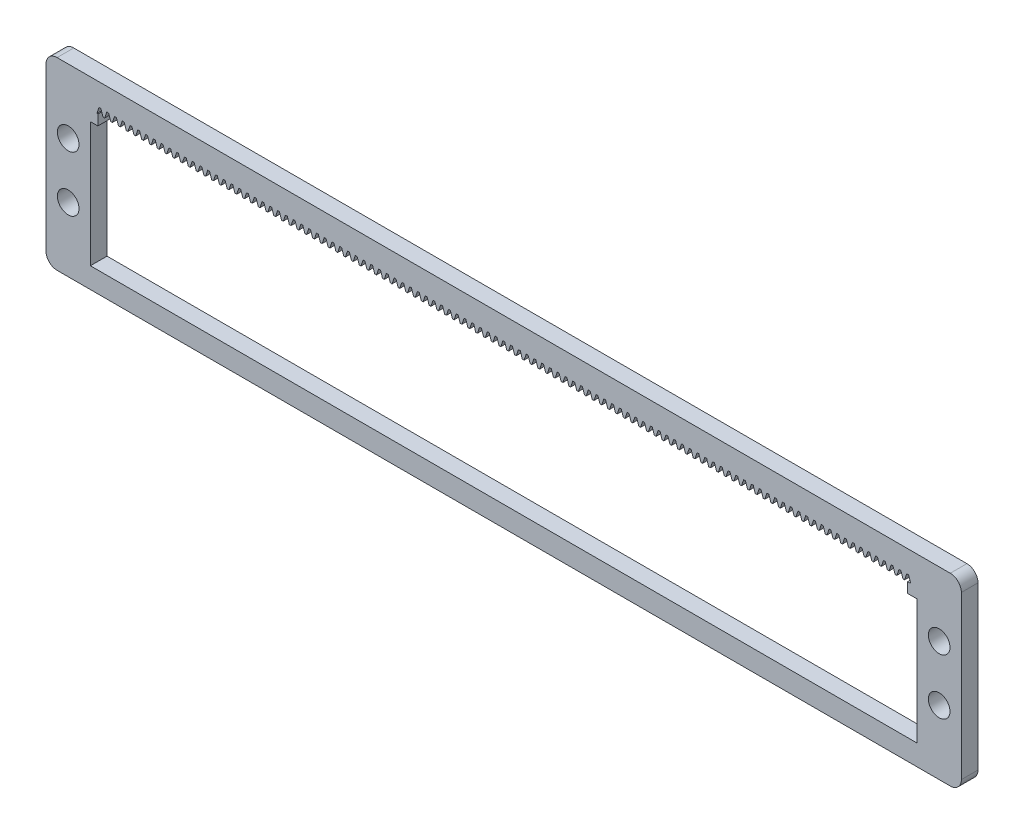
SolidWorks part; units mm, degrees
other "Markup1"
sketch "Sketch6" plane through (0, -30, 3.6) normal (0, 0, 1) x (1, 0, 0)
other "Markup2"
sketch "Sketch7" plane through (0, -30, 3.6) normal (0, 0, 1) x (1, 0, 0)
ref_plane "Front Plane" through (0, 0, 0) normal (0, 0, 1) x (1, 0, 0)
ref_plane "Top Plane" through (0, 0, 0) normal (0, 1, 0) x (1, 0, 0)
ref_plane "Right Plane" through (0, 0, 0) normal (1, 0, 0) x (0, 0, -1)
sketch "Sketch1" plane through (0, 0, 0) normal (0, 0, 1) x (1, 0, 0)
  line L1 (2, 0) -> (163, 0)
  line L2 (0, -2) -> (0, -31.22)
  line L3 (2, -33.22) -> (163, -33.22)
  line L4 (165, -2) -> (165, -31.22)
  arc A0 (163, -33.22) -> (165, -31.22) centre (163, -31.22) ccw
  arc A1 (0, -31.22) -> (2, -33.22) centre (2, -31.22) ccw
  arc A2 (2, 0) -> (0, -2) centre (2, -2) ccw
  arc A3 (163, 0) -> (165, -2) centre (163, -2) cw
  point P7 (165, -33.22)
  point P12 (0, 0)
  point P15 (165, 0)
  dimension "D3" = 2
  dimension "D1" = 33.22
  dimension "D2" = 165
extrude "Boss-Extrude1" add sketch "Sketch1" along normal blind 3
sketch "Sketch2" plane through (0, 0, 3) normal (0, 0, 1) x (1, 0, 0)
  line L0 (2, -33.22) -> (163, -33.22) construction
  line L1 (8, -7) -> (157, -7)
  line L2 (8, -7) -> (8, -29.5)
  line L3 (8, -29.5) -> (157, -29.5)
  line L4 (157, -7) -> (157, -29.5)
  line L5 (0, -2) -> (0, -31.22) construction
  line L7 (165, -31.22) -> (165, -2) construction
  line L8 (8, -18.25) -> (157, -18.25) construction
  line L12 (8, -29.5) -> (157, -29.5) construction
  line L13 (157, -4.3144) -> (157, -29.5) construction
  dimension "D1" = 22.5
  dimension "D2" = 8
  dimension "D3" = 8
  dimension "D4" = 3.72
extrude "Cut-Extrude1" cut sketch "Sketch2" against normal through all
sketch "Sketch3" plane through (0, 0, 3) normal (0, 0, 1) x (1, 0, 0)
  line L0 (157, -7) -> (8, -7) construction
  line L1 (9.35, -7) -> (155.32, -7)
  line L2 (9.35, -7) -> (9.35, -5.15)
  line L3 (9.35, -5.15) -> (155.32, -5.15)
  line L4 (155.32, -7) -> (155.32, -5.15)
  line L5 (157, -29.5) -> (157, -7) construction
  line L6 (8, -7) -> (8, -29.5) construction
  dimension "D1" = 1.85
  dimension "D2" = 1.68
  dimension "D3" = 1.35
extrude "Cut-Extrude2" cut sketch "Sketch3" against normal through all
sketch "Sketch4" plane through (0, 0, 3) normal (0, 0, 1) x (1, 0, 0)
  line L0 (156.345, -5.15) -> (155.865, -5.15) construction
  line L1 (155.32, -5.15) -> (9.35, -5.15) construction
  line L2 (156.345, -5.15) -> (156.725, -4.0118) construction
  line L3 (156.725, -4.0118) -> (155.485, -4.0118) construction
  line L4 (155.485, -4.0118) -> (155.865, -5.15)
  line L5 (155.485, -4.0118) -> (155.155, -4.0118)
  line L6 (155.155, -4.0118) -> (154.775, -5.15)
  line L7 (154.775, -5.15) -> (155.865, -5.15)
  line L10 (155.865, -5.15) -> (156.345, -5.15) construction
  dimension "D1" = 0.48
  dimension "D2" = 1.2
  dimension "D3" = 1.2
  dimension "D4" = 0.33
  dimension "D5" = 1.24
  dimension "D6" = 1.2
extrude "Cut-Extrude4" cut sketch "Sketch4" against normal through all
pattern_linear "LPattern1" count 105 spacing 1.4 along (-1, 0, 0) of "Cut-Extrude4"
sketch "Sketch5" plane through (0, 0, 3) normal (0, 0, 1) x (1, 0, 0)
  line L0 (157, -16.61) -> (165, -16.61) construction
  line L1 (163, 0) -> (2, 0) construction
  line L2 (8, -7) -> (8, -29.5) construction
  line L3 (0, -2) -> (0, -31.22) construction
  line L4 (2, -33.22) -> (163, -33.22) construction
  line L5 (0, -16.61) -> (8, -16.61) construction
  line L7 (161, -11.61) -> (161, -21.61) construction
  line L8 (4, -11.61) -> (4, -21.61) construction
  line L9 (157, -29.5) -> (157, -7) construction
  line L10 (165, -31.22) -> (165, -2) construction
  circle A4 centre (4, -11.61) radius 1.95
  circle A5 centre (4, -21.61) radius 1.95
  circle A6 centre (161, -11.61) radius 1.95
  circle A7 centre (161, -21.61) radius 1.95
  point P8 (161, -16.61)
  point P18 (4, -16.61)
  point P31 (161, -16.61)
  dimension "D1" = 3.9
  dimension "D2" = 4
  dimension "D3" = 3.9
  dimension "D4" = 3.9
  dimension "D6" = 3.9
  dimension "D5" = 10
  dimension "D7" = 10
extrude "Cut-Extrude5" cut sketch "Sketch5" against normal blind 10
